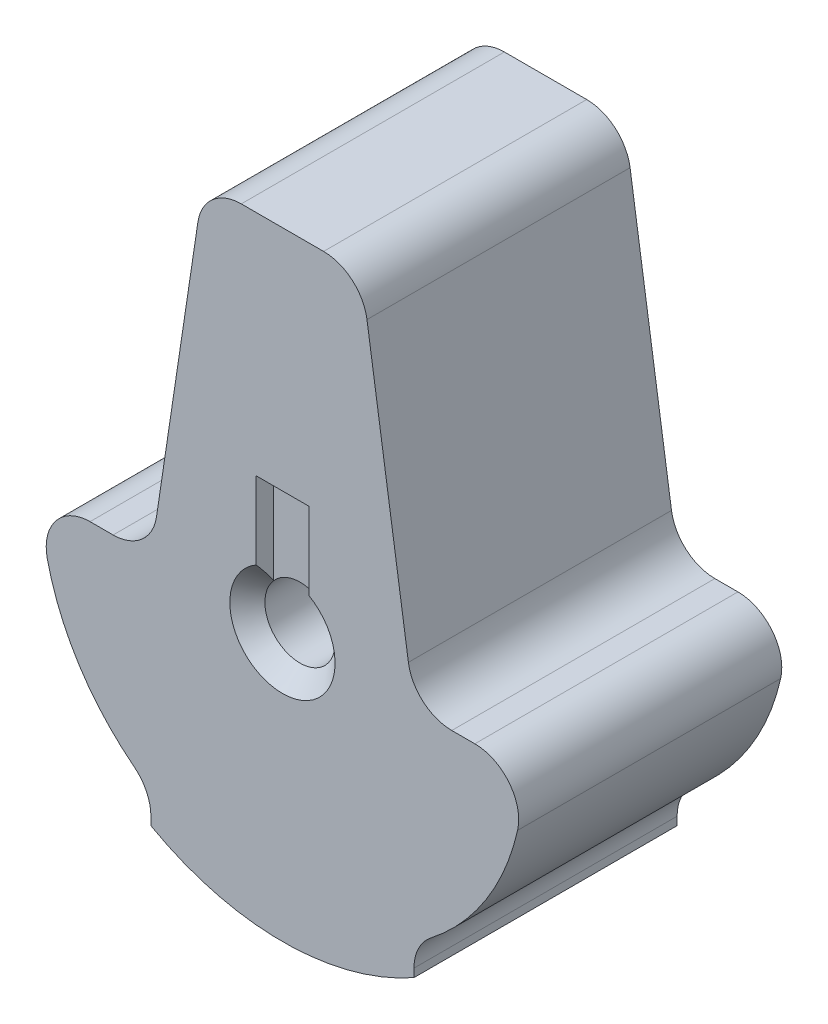
SolidWorks part; units mm, degrees
ref_plane "Front Plane" through (0, 0, 0) normal (0, 0, 1) x (1, 0, 0)
ref_plane "Top Plane" through (0, 0, 0) normal (0, 1, 0) x (1, 0, 0)
ref_plane "Right Plane" through (0, 0, 0) normal (1, 0, 0) x (0, 0, -1)
sketch "Sketch2" plane through (0, 0, 0) normal (0, 0, 1) x (1, 0, 0)
  line L5 (-0.762, 0) -> (0.762, 0)
  line L6 (-3.81, 0) -> (3.81, 0)
  line L13 (-3.81, 0) -> (-3.81, 8.636)
  line L14 (-2.286, 10.16) -> (2.286, 10.16)
  line L15 (3.81, 0) -> (3.81, 8.636)
  line L16 (-0.762, 0) -> (-0.762, 3.556)
  line L17 (-0.762, 3.556) -> (0.762, 3.556)
  line L18 (0.762, 0) -> (0.762, 3.556)
  circle A0 centre (0, 0) radius 1.524
  circle A1 centre (0, 0) radius 1.016
  circle A2 centre (0, 0) radius 3.81
  arc A3 (3.81, 8.636) -> (2.286, 10.16) centre (2.286, 8.636) ccw
  arc A4 (-3.81, 8.636) -> (-2.286, 10.16) centre (-2.286, 8.636) cw
  point P0 (0, 0)
  point P5 (0, 0)
  dimension "D1" = 2.032
  dimension "D2" = 3.048
  dimension "D5" = 7.62
  dimension "D7" = 1.524
  dimension "D3" = 1.524
  dimension "D4" = 3.556
  dimension "D6" = 10.16
extrude "Boss-Extrude2" add sketch "Sketch2" along normal blind 7.62 contours L6 A2 A0 | A1 L6 A0 | A1 L6 A0 L18 | A1 L18 A0 L16 | A1 L16 A0 L6 | L16 A2 L6 A0 | L18 A2 L16 A0 | L6 A2 L18 A0 | A2 L15 L14 L13 L16 L17 L18 | A2 L18 L17 L16
sketch "Sketch3" plane through (0, 0, 7.62) normal (0, 0, 1) x (1, 0, 0)
  line L4 (-3.81, 0) -> (3.81, 0)
  line L5 (-3.81, 8.636) -> (-3.81, 0)
  line L6 (2.286, 10.16) -> (-2.286, 10.16)
  line L7 (3.81, 0) -> (3.81, 8.636)
  line L8 (-3.81, 0) -> (3.81, 0)
  line L9 (-3.81, 8.636) -> (-3.81, 0)
  line L10 (2.286, 10.16) -> (-2.286, 10.16)
  line L11 (3.81, 0) -> (3.81, 8.636)
  line L12 (-0.762, 0) -> (0.762, 0)
  line L13 (-0.762, 3.556) -> (-0.762, 0)
  line L14 (0.762, 3.556) -> (-0.762, 3.556)
  line L15 (0.762, 0) -> (0.762, 3.556)
  line L16 (-0.762, 0) -> (0.762, 0)
  line L17 (-0.762, 3.556) -> (-0.762, 0)
  line L18 (0.762, 3.556) -> (-0.762, 3.556)
  line L19 (0.762, 0) -> (0.762, 3.556)
  circle A1 centre (0, 0) radius 3.81
  circle A2 centre (0, 0) radius 3.81
  circle A3 centre (0, 0) radius 1.016
  circle A4 centre (0, 0) radius 1.016
  circle A5 centre (0, 0) radius 1.524
  circle A6 centre (0, 0) radius 1.524
  arc A8 (3.81, 8.636) -> (2.286, 10.16) centre (2.286, 8.636) ccw
  arc A9 (3.81, 8.636) -> (2.286, 10.16) centre (2.286, 8.636) ccw
  arc A10 (-2.286, 10.16) -> (-3.81, 8.636) centre (-2.286, 8.636) ccw
  arc A11 (-2.286, 10.16) -> (-3.81, 8.636) centre (-2.286, 8.636) ccw
  arc M16 (1.016, 0) -> (-0.762, 0.672) centre (0, 0) cw
  dimension "D1" = 0
  dimension "D2" = 0
  dimension "D3" = 0
  dimension "D4" = 0
  dimension "D5" = 0
extrude "Cut-Extrude1" cut sketch "Sketch3" against normal blind 0.508 contours A2 L19 L18 L17 | L19 A6 L17 M16 | A4
sketch "Sketch4" plane through (0, 0, 0) normal (0, 0, -1) x (-1, 0, 0)
  line L3 (3.81, 0) -> (3.81, 8.636)
  line L4 (2.286, 10.16) -> (-2.286, 10.16)
  line L5 (-3.81, 8.636) -> (-3.81, 0)
  line L6 (3.81, 0) -> (3.81, 8.636)
  line L7 (2.286, 10.16) -> (-2.286, 10.16)
  line L8 (-3.81, 8.636) -> (-3.81, 0)
  line L10 (-3.81, 0) -> (3.81, 0)
  line L11 (3.81, 0) -> (3.81, 8.636)
  line L12 (2.286, 10.16) -> (-2.286, 10.16)
  line L13 (-3.81, 8.636) -> (-3.81, 0)
  line L14 (-3.81, 0) -> (3.81, 0)
  line L15 (3.81, 0) -> (3.81, 8.636)
  line L16 (2.286, 10.16) -> (-2.286, 10.16)
  line L17 (-3.81, 8.636) -> (-3.81, 0)
  line L18 (-0.762, 0) -> (0.762, 0)
  line L19 (0.762, 0) -> (0.762, 3.556)
  line L20 (0.762, 3.556) -> (-0.762, 3.556)
  line L21 (-0.762, 3.556) -> (-0.762, 0)
  line L22 (-0.762, 0) -> (0.762, 0)
  line L23 (0.762, 0) -> (0.762, 3.556)
  line L24 (0.762, 3.556) -> (-0.762, 3.556)
  line L25 (-0.762, 3.556) -> (-0.762, 0)
  arc A1 (-3.81, 0) -> (3.81, 0) centre (0, 0) ccw
  arc A2 (-3.81, 0) -> (3.81, 0) centre (0, 0) ccw
  circle A3 centre (0, 0) radius 3.81
  circle A4 centre (0, 0) radius 3.81
  circle A5 centre (0, 0) radius 1.016
  circle A6 centre (0, 0) radius 1.016
  circle A7 centre (0, 0) radius 1.524
  circle A8 centre (0, 0) radius 1.524
  arc A10 (-2.286, 10.16) -> (-3.81, 8.636) centre (-2.286, 8.636) ccw
  arc A11 (3.81, 8.636) -> (2.286, 10.16) centre (2.286, 8.636) ccw
  arc A12 (3.81, 8.636) -> (2.286, 10.16) centre (2.286, 8.636) ccw
  arc A13 (-2.286, 10.16) -> (-3.81, 8.636) centre (-2.286, 8.636) ccw
  arc A14 (-2.286, 10.16) -> (-3.81, 8.636) centre (-2.286, 8.636) ccw
  arc A15 (-2.286, 10.16) -> (-3.81, 8.636) centre (-2.286, 8.636) ccw
  arc A16 (3.81, 8.636) -> (2.286, 10.16) centre (2.286, 8.636) ccw
  arc A17 (3.81, 8.636) -> (2.286, 10.16) centre (2.286, 8.636) ccw
  arc M20 (0.762, 0.672) -> (-1.016, 0) centre (0, 0) cw
  dimension "D1" = 0
  dimension "D2" = 0
  dimension "D3" = 0
  dimension "D4" = 0
  dimension "D5" = 0
  dimension "D6" = 0
extrude "Cut-Extrude2" cut sketch "Sketch4" against normal blind 0.508 contours A8 L23 A4 L25 | L23 A8 L25 M20
sketch "Sketch7" plane through (0, 0, 0) normal (0, 1, 0) x (1, 0, 0)
  line L0 (0, 0) -> (0, -7.62)
  line L1 (-2.286, -7.62) -> (2.286, -7.62) construction
  line L2 (0, -7.62) -> (1.524, -7.62)
  line L3 (1.524, -7.62) -> (1.016, -7.112)
  line L4 (1.016, -7.112) -> (1.016, -0.508)
  line L5 (1.016, -0.508) -> (1.524, 0)
  line L6 (-2.286, 0) -> (2.286, 0) construction
  line L7 (1.524, 0) -> (0, 0)
  point P5 (1.016, -3.81)
  point P12 (0, -3.81)
  dimension "D1" = 1.016
  dimension "D2" = 45
  dimension "D4" = 1.524
revolve "Cut-Revolve1" cut sketch "Sketch7" angle 360 about L0
sketch "Sketch10" plane through (0, 0, 7.62) normal (0, 0, 1) x (1, 0, 0)
  line L0 (-6.985, 0) -> (6.985, 0)
  line L4 (3.81, 0) -> (3.81, 8.636)
  line L5 (3.81, 0) -> (3.81, 8.636)
  line L6 (2.286, 10.16) -> (-2.286, 10.16)
  line L9 (2.286, 10.16) -> (-2.286, 10.16)
  line L10 (-3.81, 8.636) -> (-3.81, 0)
  line L11 (-3.81, 8.636) -> (-3.81, 0)
  circle A0 centre (0, 0) radius 6.985
  arc A2 (-3.81, 0) -> (3.81, 0) centre (0, 0) ccw
  arc A3 (-3.81, 0) -> (3.81, 0) centre (0, 0) ccw
  arc A6 (3.81, 8.636) -> (2.286, 10.16) centre (2.286, 8.636) ccw
  arc A7 (3.81, 8.636) -> (2.286, 10.16) centre (2.286, 8.636) ccw
  arc A8 (-2.286, 10.16) -> (-3.81, 8.636) centre (-2.286, 8.636) ccw
  arc A9 (-2.286, 10.16) -> (-3.81, 8.636) centre (-2.286, 8.636) ccw
  arc M7 (-3.81, 0) -> (3.81, 0) centre (0, 0) ccw
  dimension "D1" = 13.97
  dimension "D2" = 0
extrude "Boss-Extrude8" add sketch "Sketch10" against normal up to surface (7.62 mm away) contours L0 A0 M7 up to face at (0, 1.727, 0)
sketch "Sketch14" plane through (0, 0, 7.62) normal (0, 0, 1) x (1, 0, 0)
  line L0 (-3.81, 0) -> (-3.81, -6.7454)
  line L1 (3.81, 0) -> (3.81, -6.7454)
  line L5 (-3.81, 8.636) -> (-3.81, 0)
  line L6 (-3.81, 0) -> (-6.985, 0)
  line L7 (6.985, 0) -> (3.81, 0)
  line L8 (3.81, 0) -> (3.81, 8.636)
  line L9 (2.286, 10.16) -> (-2.286, 10.16)
  line L10 (-3.81, 8.636) -> (-3.81, 0)
  line L11 (-3.81, 0) -> (-6.985, 0)
  line L12 (6.985, 0) -> (3.81, 0)
  line L13 (3.81, 0) -> (3.81, 8.636)
  line L14 (2.286, 10.16) -> (-2.286, 10.16)
  circle A0 centre (0, 0) radius 7.747
  arc A3 (-6.985, 0) -> (6.985, 0) centre (0, 0) ccw
  arc A4 (3.81, 8.636) -> (2.286, 10.16) centre (2.286, 8.636) ccw
  arc A5 (-2.286, 10.16) -> (-3.81, 8.636) centre (-2.286, 8.636) ccw
  arc A6 (-6.985, 0) -> (6.985, 0) centre (0, 0) ccw
  arc A7 (3.81, 8.636) -> (2.286, 10.16) centre (2.286, 8.636) ccw
  arc A8 (-2.286, 10.16) -> (-3.81, 8.636) centre (-2.286, 8.636) ccw
  arc M16 (-6.985, 0) -> (6.985, 0) centre (0, 0) ccw
  dimension "D2" = 15.494
  dimension "D1" = 0
extrude "Boss-Extrude10" add sketch "Sketch14" against normal up to surface (7.62 mm away) contours L0 A0 L1 M16 up to face at (0, 1.727, 0)
fillet "Fillet2" radius 1.27 2 edges at (-6.985, 0, 3.81) (6.985, 0, 3.81)
sketch "Sketch16" plane through (0, 0, 7.62) normal (0, 0, 1) x (1, 0, 0)
  line L0 (-3.81, 0) -> (-2.286, 10.16)
  line L1 (2.286, 10.16) -> (3.81, 0)
  line L7 (-3.81, 0) -> (-5.5721, 0)
  line L8 (-3.81, -5.8544) -> (-3.81, -6.7454)
  line L9 (3.81, -6.7454) -> (3.81, -5.8544)
  line L10 (5.5721, 0) -> (3.81, 0)
  line L11 (3.81, 0) -> (3.81, 8.636)
  line L12 (2.286, 10.16) -> (-2.286, 10.16)
  line L13 (-3.81, 8.636) -> (-3.81, 0)
  line L14 (-3.81, 0) -> (-5.5721, 0)
  line L15 (-3.81, -5.8544) -> (-3.81, -6.7454)
  line L16 (3.81, -6.7454) -> (3.81, -5.8544)
  line L17 (5.5721, 0) -> (3.81, 0)
  line L18 (3.81, 0) -> (3.81, 8.636)
  line L19 (2.286, 10.16) -> (-2.286, 10.16)
  line L20 (-3.81, 8.636) -> (-3.81, 0)
  arc A7 (-5.5721, 0) -> (-6.8103, -1.5522) centre (-5.5721, -1.27) ccw
  arc A8 (-6.8103, -1.5522) -> (-3.81, -5.8544) centre (0, 0) ccw
  arc A9 (-3.81, -6.7454) -> (3.81, -6.7454) centre (0, 0) ccw
  arc A10 (3.81, -5.8544) -> (6.8103, -1.5522) centre (0, 0) ccw
  arc A11 (6.8103, -1.5522) -> (5.5721, 0) centre (5.5721, -1.27) ccw
  arc A12 (3.81, 8.636) -> (2.286, 10.16) centre (2.286, 8.636) ccw
  arc A13 (-2.286, 10.16) -> (-3.81, 8.636) centre (-2.286, 8.636) ccw
  arc A14 (-5.5721, 0) -> (-6.8103, -1.5522) centre (-5.5721, -1.27) ccw
  arc A15 (-6.8103, -1.5522) -> (-3.81, -5.8544) centre (0, 0) ccw
  arc A16 (-3.81, -6.7454) -> (3.81, -6.7454) centre (0, 0) ccw
  arc A17 (3.81, -5.8544) -> (6.8103, -1.5522) centre (0, 0) ccw
  arc A18 (6.8103, -1.5522) -> (5.5721, 0) centre (5.5721, -1.27) ccw
  arc A19 (3.81, 8.636) -> (2.286, 10.16) centre (2.286, 8.636) ccw
  arc A20 (-2.286, 10.16) -> (-3.81, 8.636) centre (-2.286, 8.636) ccw
  line M28 (3.81, 0) -> (3.81, 8.636)
  arc M29 (3.81, 8.636) -> (2.286, 10.16) centre (2.286, 8.636) ccw
  arc M31 (-2.286, 10.16) -> (-3.81, 8.636) centre (-2.286, 8.636) ccw
  line M32 (-3.81, 8.636) -> (-3.81, 0)
  dimension "D1" = 0
extrude "Cut-Extrude4" cut sketch "Sketch16" against normal up to surface (7.62 mm away) contours L0 M32 M31 | L1 M29 M28 up to face at (0, 1.727, 0)
fillet "Fillet4" radius 1.27 6 edges at (-3.81, -5.8544, 3.81) (3.81, -5.8544, 3.81) (3.81, 0, 3.81) (-3.81, 0, 3.81) (2.286, 10.16, 3.81) (-2.286, 10.16, 3.81)
